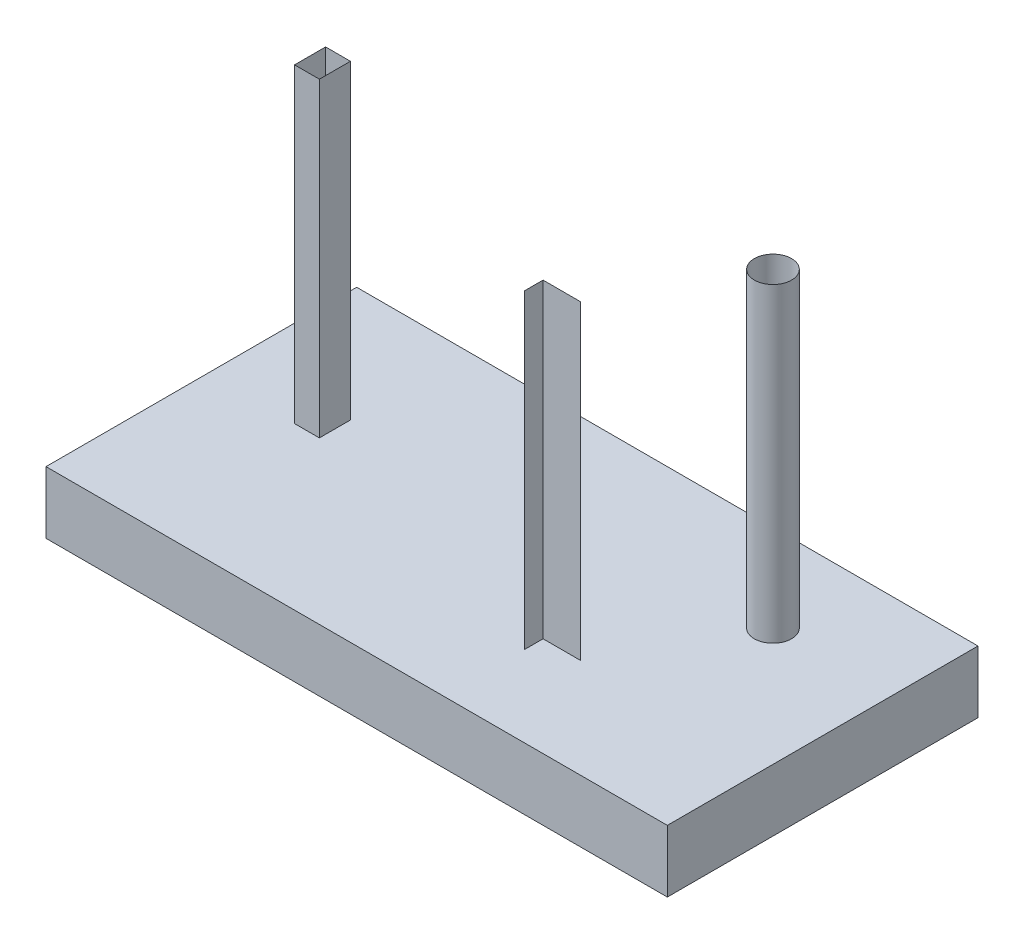
SolidWorks part; units mm, degrees
ref_plane "Face" through (0, 0, 0) normal (0, 0, 1) x (1, 0, 0)
ref_plane "Dessus" through (0, 0, 0) normal (0, 1, 0) x (1, 0, 0)
ref_plane "Droite" through (0, 0, 0) normal (1, 0, 0) x (0, 0, -1)
sketch "Sketch1" plane through (0, 0, 0) normal (0, 1, 0) x (1, 0, 0)
  line L1 (0, 0) -> (100, 0)
  line L2 (0, 0) -> (0, 50)
  line L3 (0, 50) -> (100, 50)
  line L4 (100, 0) -> (100, 50)
  dimension "D1" = 50
  dimension "D2" = 100
extrude "Extrude1" add sketch "Sketch1" along normal blind 10
sketch "Sketch2" plane through (0, 10, 0) normal (0, 1, 0) x (-1, 0, 0)
  line L0 (-71, -15) -> (-65, -15)
  line L1 (-65, -15) -> (-65, -12)
  line L2 (-100, -50) -> (0, -50) construction
  line L3 (-19, -30) -> (-15, -30)
  line L4 (-19, -30) -> (-19, -25)
  line L5 (-19, -25) -> (-15, -25)
  line L6 (-15, -30) -> (-15, -25)
  line L7 (-100, 0) -> (-100, -50) construction
  line L8 (0, -50) -> (0, 0) construction
  circle A0 centre (-82, -35) radius 3
  dimension "D1" = 6
  dimension "D2" = 6
  dimension "D3" = 3
  dimension "D4" = 5
  dimension "D5" = 4
  dimension "D6" = 15
  dimension "D7" = 18
  dimension "D8" = 35
  dimension "D9" = 35
  dimension "D10" = 15
  dimension "D11" = 20
surface "Surface-Extrude1" sketch "Sketch2" parameters "D1"=50, "D19"=1
sketch "Sketch3" plane through (0, 0, 0) normal (0, -1, 0) x (1, 0, 0)
  line L0 (0, -50) -> (0, 0) construction
  line L1 (25, -33) -> (35, -33)
  line L2 (25, -33) -> (25, -25)
  line L3 (25, -25) -> (35, -25)
  line L4 (35, -33) -> (35, -25)
  line L5 (0, 0) -> (100, 0) construction
  dimension "D1" = 25
  dimension "D2" = 8
  dimension "D3" = 10
  dimension "D4" = 25
split line "Split Line1"
